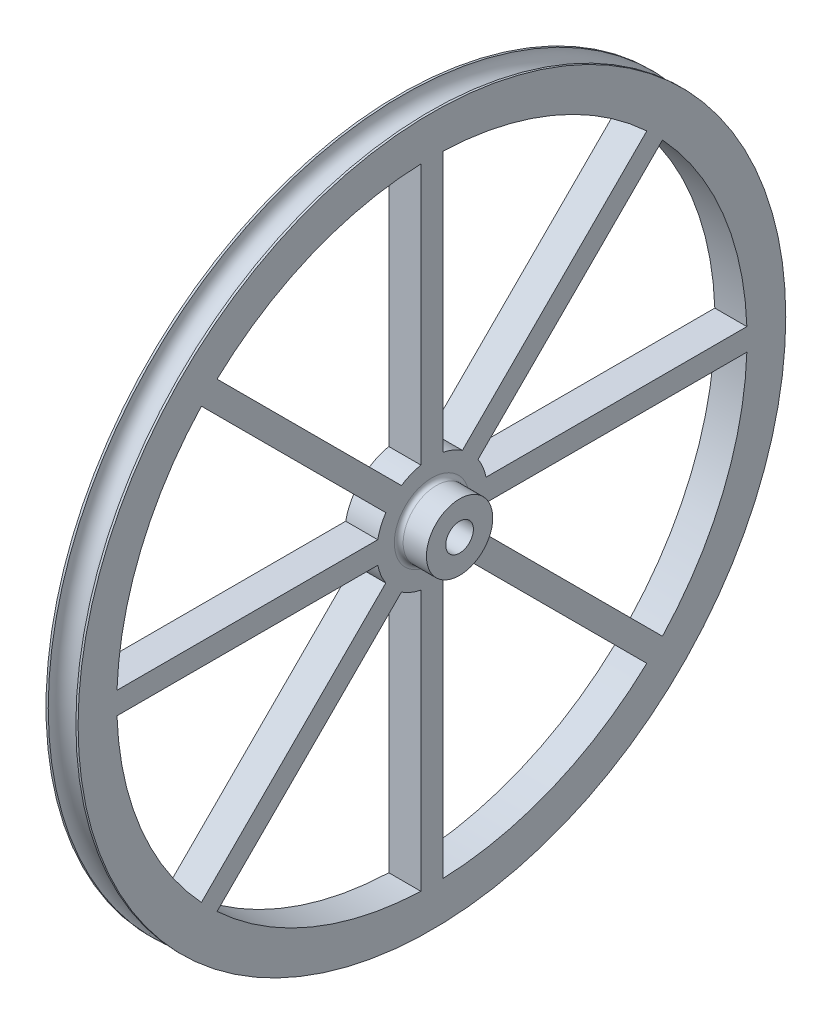
SolidWorks part; units mm, degrees
ref_plane "Front Plane" through (0, 0, 0) normal (0, 0, 1) x (1, 0, 0)
ref_plane "Top Plane" through (0, 0, 0) normal (0, 1, 0) x (1, 0, 0)
ref_plane "Right Plane" through (0, 0, 0) normal (1, 0, 0) x (0, 0, -1)
sketch "Sketch1" plane through (0, 0, 0) normal (1, 0, 0) x (0, 0, -1)
  circle A0 centre (0, 0) radius 40.64
  dimension "D1" = 81.28
extrude "Boss-Extrude1" add sketch "Sketch1" along normal blind 3.683
sketch "Sketch10" plane through (0, 0, 0) normal (0, 0, 1) x (1, 0, 0)
  line L0 (3.683, 40.64) -> (0, 40.64) construction
  line L1 (-1.0162, 0) -> (5.466, 0) construction
  line L2 (55, 0) -> (-55, 0) construction
  circle A0 centre (1.8415, 40.64) radius 1.5875
  dimension "D1" = 3.175
revolve "Cut-Revolve1" cut sketch "Sketch10" angle 360 about L1
sketch "Sketch11" plane through (3.683, 0, 0) normal (1, 0, 0) x (0, 0, -1)
  line L2 (0, -50.6508) -> (0, 43.6326) construction
  line L3 (-53.144, 0) -> (6.35, 0) construction
  line L4 (-1.27, 36.1727) -> (-1.27, 6.2217)
  line L5 (1.27, 36.1727) -> (1.27, 6.2217)
  line L6 (24.6799, 26.476) -> (3.5014, 5.2974)
  line L7 (26.476, 24.6799) -> (5.2974, 3.5014)
  line L8 (36.1727, 1.27) -> (6.2217, 1.27)
  line L9 (36.1727, -1.27) -> (6.2217, -1.27)
  line L10 (26.476, -24.6799) -> (5.2974, -3.5014)
  line L11 (24.6799, -26.476) -> (3.5014, -5.2974)
  line L12 (1.27, -36.1727) -> (1.27, -6.2217)
  line L13 (-1.27, -36.1727) -> (-1.27, -6.2217)
  line L14 (-24.6799, -26.476) -> (-3.5014, -5.2974)
  line L15 (-26.476, -24.6799) -> (-5.2974, -3.5014)
  line L16 (-36.1727, -1.27) -> (-6.2217, -1.27)
  line L17 (-36.1727, 1.27) -> (-6.2217, 1.27)
  line L18 (-26.476, 24.6799) -> (-5.2974, 3.5014)
  line L19 (-24.6799, 26.476) -> (-3.5014, 5.2974)
  arc A2 (5.2974, -3.5014) -> (6.2217, -1.27) centre (0, 0) ccw
  arc A3 (-26.476, 24.6799) -> (-36.1727, 1.27) centre (0, 0) ccw
  arc A4 (24.6799, 26.476) -> (1.27, 36.1727) centre (0, 0) ccw
  arc A5 (-1.27, 36.1727) -> (-24.6799, 26.476) centre (0, 0) ccw
  arc A6 (36.1727, 1.27) -> (26.476, 24.6799) centre (0, 0) ccw
  arc A7 (26.476, -24.6799) -> (36.1727, -1.27) centre (0, 0) ccw
  arc A8 (1.27, -36.1727) -> (24.6799, -26.476) centre (0, 0) ccw
  arc A9 (-24.6799, -26.476) -> (-1.27, -36.1727) centre (0, 0) ccw
  arc A10 (-36.1727, -1.27) -> (-26.476, -24.6799) centre (0, 0) ccw
  arc A11 (1.27, -6.2217) -> (3.5014, -5.2974) centre (0, 0) ccw
  arc A12 (-3.5014, -5.2974) -> (-1.27, -6.2217) centre (0, 0) ccw
  arc A13 (-6.2217, -1.27) -> (-5.2974, -3.5014) centre (0, 0) ccw
  arc A14 (-5.2974, 3.5014) -> (-6.2217, 1.27) centre (0, 0) ccw
  arc A15 (-1.27, 6.2217) -> (-3.5014, 5.2974) centre (0, 0) ccw
  arc A16 (3.5014, 5.2974) -> (1.27, 6.2217) centre (0, 0) ccw
  arc A17 (6.2217, 1.27) -> (5.2974, 3.5014) centre (0, 0) ccw
  point P43 (0, 0)
  dimension "D1" = 12.7
  dimension "D2" = 72.39
  dimension "D3" = 2.54
  dimension "D4" = 1.27
  dimension "D5" = 8
extrude "Cut-Extrude3" cut sketch "Sketch11" against normal through all
sketch "Sketch12" plane through (3.683, 0, 0) normal (1, 0, 0) x (0, 0, -1)
  circle A0 centre (0, 0) radius 1.5875
  dimension "D1" = 3.175
extrude "Cut-Extrude4" cut sketch "Sketch12" against normal through all
sketch "Sketch13" plane through (3.683, 0, 0) normal (1, 0, 0) x (0, 0, -1)
  circle A0 centre (0, 0) radius 3.81
  circle A1 centre (0, 0) radius 1.5875
  circle A2 centre (0, 0) radius 1.5875 construction
  dimension "D1" = 7.62
extrude "Boss-Extrude2" add sketch "Sketch13" along normal blind 3.175
fillet "Fillet1" radius 0.508 1 edges at (3.683, 0, -3.81)
